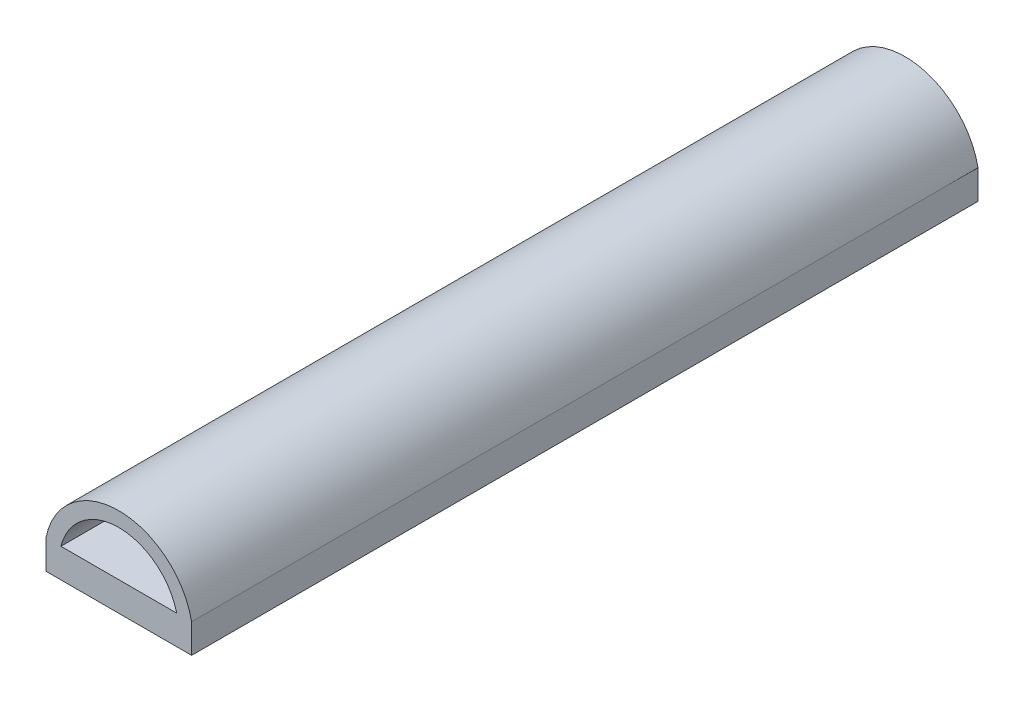
SolidWorks part; units mm, degrees
ref_plane "Front Plane" through (0, 0, 0) normal (0, 0, 1) x (1, 0, 0)
ref_plane "Top Plane" through (0, 0, 0) normal (0, 1, 0) x (1, 0, 0)
ref_plane "Right Plane" through (0, 0, 0) normal (1, 0, 0) x (0, 0, -1)
sketch "Sketch1" plane through (0, 0, 0) normal (0, 0, 1) x (1, 0, 0)
  line L0 (-6.35, 1.2591) -> (-6.35, -1.2809)
  line L1 (-6.35, -1.2809) -> (6.35, -1.2809)
  line L3 (6.35, -1.2809) -> (6.35, 1.2591)
  line L39 (-5.049, 1.2591) -> (5.049, 1.2591)
  arc A0 (-6.35, 1.2591) -> (6.35, 1.2591) centre (0, 0) cw
  arc A3 (-5.049, 1.2591) -> (5.049, 1.2591) centre (0, 0) cw
  dimension "D2" = 1.27
  dimension "D4" = 6.4736
  dimension "D1" = 12.7
  dimension "D3" = 2.54
extrude "Boss-Extrude1" add sketch "Sketch1" along normal blind 68.58
sketch "Sketch3" plane through (0, 0, 0) normal (0, 0, -1) x (-1, 0, 0)
  line L0 (0.508, -1.2809) -> (0.508, -3.3764)
  line L1 (0.508, -3.3764) -> (1.0795, -3.3764)
  line L2 (1.0795, -3.3764) -> (1.0795, -4.2654)
  line L3 (1.0795, -4.2654) -> (-1.0795, -4.2654)
  line L4 (-1.0795, -4.2654) -> (-1.0795, -3.3764)
  line L5 (-1.0795, -3.3764) -> (-0.508, -3.3764)
  line L6 (-0.508, -3.3764) -> (-0.508, -1.2809)
  line L7 (-0.508, -1.2809) -> (0.508, -1.2809)
  line L9 (6.35, -1.2809) -> (-6.35, -1.2809) construction
  point P10 (0, -1.2809)
  dimension "D1" = 2.0955
  dimension "D2" = 2.159
  dimension "D3" = 1.016
  dimension "D4" = 0.889
extrude "Boss-Extrude2" add sketch "Sketch3" against normal blind 25.4
